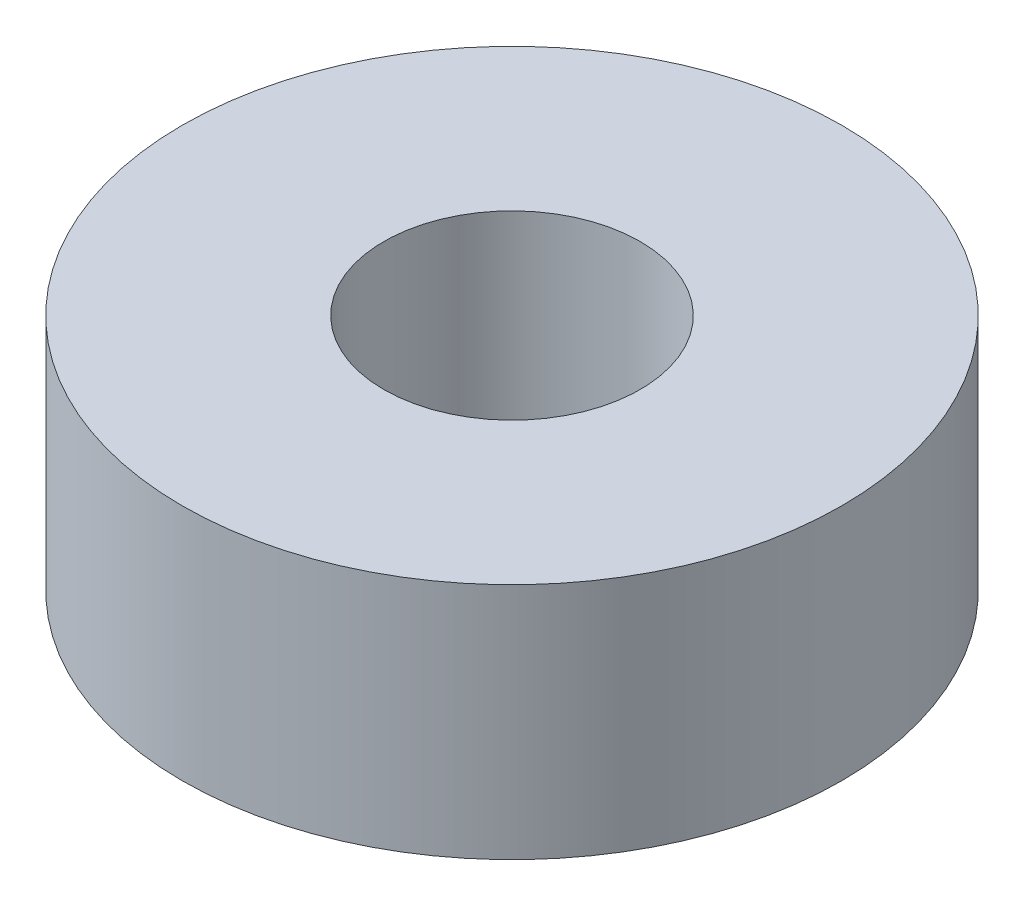
SolidWorks part; units mm, degrees
material "A3钢"
ref_plane "前视基准面" through (0, 0, 0) normal (0, 0, 1) x (1, 0, 0)
ref_plane "上视基准面" through (0, 0, 0) normal (0, 1, 0) x (1, 0, 0)
ref_plane "右视基准面" through (0, 0, 0) normal (1, 0, 0) x (0, 0, -1)
sketch "草图1" plane through (0, 0, 0) normal (0, 1, 0) x (1, 0, 0)
  circle A0 centre (0, 0) radius 9
  circle A1 centre (0, 0) radius 3.5
  dimension "D1" = 18
  dimension "D2" = 7
extrude "凸台-拉伸1" add sketch "草图1" along normal mid plane 6.5
